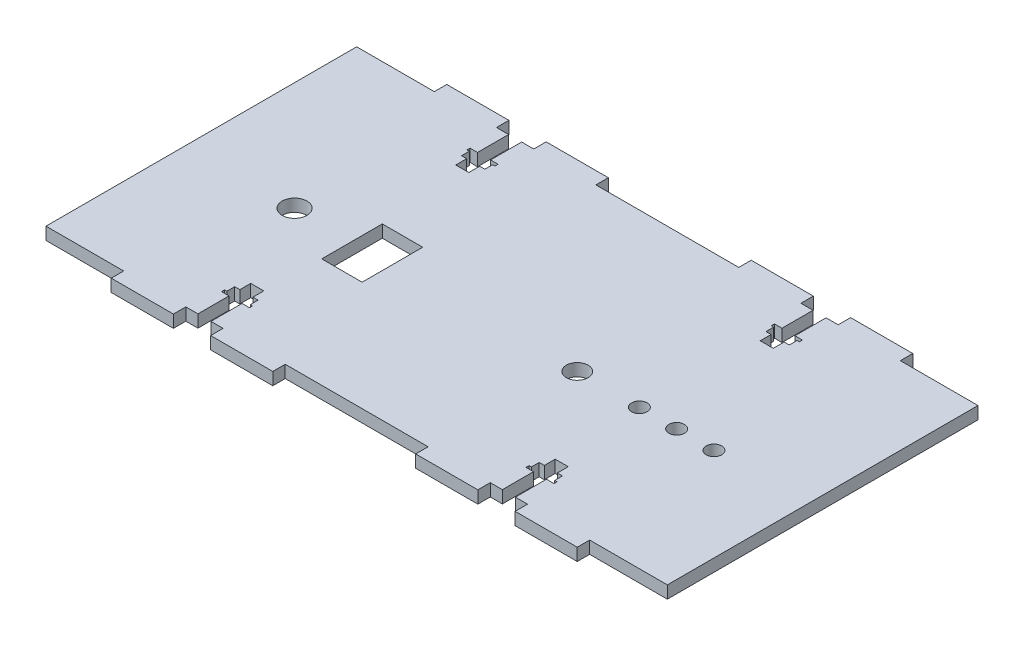
SolidWorks part; units mm, degrees
ref_plane "Front Plane" through (0, 0, 0) normal (0, 0, 1) x (1, 0, 0)
ref_plane "Top Plane" through (0, 0, 0) normal (0, 1, 0) x (1, 0, 0)
ref_plane "Right Plane" through (0, 0, 0) normal (1, 0, 0) x (0, 0, -1)
sketch "Sketch1" plane through (0, 0, 0) normal (0, 1, 0) x (1, 0, 0)
  line L0 (-55, -50) -> (-43, -50)
  line L1 (0, 0) -> (199.9733, 0) construction
  line L2 (-100, -50) -> (-100, 50)
  line L3 (-100, -50) -> (-75, -50)
  line L4 (100, -50) -> (100, 50)
  line L5 (0, 0) -> (100, -50) construction
  line L6 (-100, -50) -> (0, 0) construction
  line L7 (-23, -50) -> (23, -50)
  line L8 (-75, -50) -> (-75, -54)
  line L9 (-75, -54) -> (-55, -54)
  line L10 (-55, -50) -> (-55, -54)
  line L11 (43, -50) -> (55, -50)
  line L12 (-43, -50) -> (-43, -54)
  line L13 (-43, -54) -> (-23, -54)
  line L14 (-23, -50) -> (-23, -54)
  line L15 (-100, 50) -> (0, 0) construction
  line L16 (75, -50) -> (75, -54)
  line L17 (75, -54) -> (55, -54)
  line L18 (55, -50) -> (55, -54)
  line L19 (75, -50) -> (100, -50)
  line L20 (43, -50) -> (43, -54)
  line L21 (43, -54) -> (23, -54)
  line L22 (23, -50) -> (23, -54)
  line L23 (0, 0) -> (100, 50) construction
  line L24 (23, 50) -> (23, 54)
  line L25 (43, 54) -> (23, 54)
  line L26 (43, 50) -> (43, 54)
  line L27 (75, 50) -> (100, 50)
  line L28 (55, 50) -> (55, 54)
  line L29 (75, 54) -> (55, 54)
  line L30 (75, 50) -> (75, 54)
  line L31 (-23, 50) -> (-23, 54)
  line L32 (-43, 54) -> (-23, 54)
  line L33 (-43, 50) -> (-43, 54)
  line L34 (43, 50) -> (55, 50)
  line L35 (-55, 50) -> (-55, 54)
  line L36 (-75, 54) -> (-55, 54)
  line L37 (-75, 50) -> (-75, 54)
  line L38 (-23, 50) -> (23, 50)
  line L39 (-100, 50) -> (-75, 50)
  line L40 (-55, 50) -> (-43, 50)
  point P0 (0, 0)
  point P25 (-100, 0)
  point P43 (100, 0)
  dimension "D2" = 200
  dimension "D3" = 50
  dimension "D4" = 20
  dimension "D5" = 12
  dimension "D6" = 20
  dimension "D7" = 4
  dimension "D8" = 12
  dimension "D9" = 20
  dimension "D10" = 20
  dimension "D11" = 25
  dimension "D12" = 4
  dimension "D13" = 25
extrude "Boss-Extrude1" add sketch "Sketch1" along normal blind 4
sketch "Sketch2" plane through (0, 0, 0) normal (0, -1, 0) x (1, 0, 0)
  line L0 (-100, 5) -> (100, 5) construction
  line L1 (-46.5, 14.75) -> (-33.5, 14.75)
  line L2 (-46.5, 14.75) -> (-46.5, -4.75)
  line L3 (-46.5, -4.75) -> (-33.5, -4.75)
  line L4 (-33.5, 14.75) -> (-33.5, -4.75)
  line L5 (-46.5, 14.75) -> (-33.5, -4.75) construction
  line L6 (-46.5, -4.75) -> (-33.5, 14.75) construction
  line L7 (-100, -50) -> (-100, 50) construction
  line L8 (100, 50) -> (100, -50) construction
  line L9 (-100, 50) -> (-75, 50) construction
  circle A0 centre (-65, 5) radius 4
  circle A1 centre (26, 5) radius 3.5
  circle A2 centre (46, 5) radius 2.5
  circle A3 centre (58, 5) radius 2.5
  circle A4 centre (70, 5) radius 2.5
  point P2 (-40, 5)
  dimension "D1" = 8
  dimension "D6" = 7
  dimension "D7" = 5
  dimension "D2" = 13
  dimension "D3" = 19.5
  dimension "D4" = 25
  dimension "D5" = 35
  dimension "D9" = 20
  dimension "D10" = 45
  dimension "D11" = 12
  dimension "D12" = 30
  dimension "D8" = 3
extrude "Cut-Extrude1" cut sketch "Sketch2" against normal through all
sketch "Sketch3" plane through (0, 0, 0) normal (0, -1, 0) x (1, 0, 0)
  line L0 (-43, -50) -> (-55, -50) construction
  line L1 (-51.1, -50) -> (-46.9, -50)
  line L2 (-51.1, -50) -> (-51.1, -40)
  line L3 (-51.1, -33) -> (-46.9, -33)
  line L4 (-46.9, -50) -> (-46.9, -40)
  line L5 (-55, -50) -> (-55, -54) construction
  line L6 (-49, -50) -> (-49, -33) construction
  line L7 (-52.75, -36.5) -> (-51.1, -36.5)
  line L8 (-52.75, -36.5) -> (-52.75, -39)
  line L9 (-46.9, -36.5) -> (-46.9, -33)
  line L10 (-45.25, -36.5) -> (-45.25, -39)
  line L11 (-53.5, -39) -> (-53.5, -40)
  line L12 (-44.5, -40) -> (-46.9, -40)
  line L13 (0, -50) -> (0, -26.0736) construction
  line L14 (23, -50) -> (-23, -50) construction
  line L15 (-46.9, -40) -> (-44.5, -40)
  line L16 (-44.5, -39) -> (-44.5, -40)
  line L17 (-44.5, -39) -> (-45.25, -39)
  line L18 (-46.9, -36.5) -> (-46.9, -33)
  line L19 (-45.25, -39) -> (-44.5, -39)
  line L20 (-51.1, -36.5) -> (-52.75, -36.5)
  line L21 (-52.75, -39) -> (-53.5, -39)
  line L22 (-46.9, -36.5) -> (-45.25, -36.5)
  line L23 (-51.1, -36.5) -> (-51.1, -33)
  line L24 (-51.1, -40) -> (-53.5, -40)
  line L25 (-52.75, -36.5) -> (-52.75, -39)
  line L26 (-51.1, -36.5) -> (-51.1, -33)
  line L27 (-53.5, -39) -> (-52.75, -39)
  line L28 (-53.5, -39) -> (-53.5, -40)
  line L29 (-53.5, -40) -> (-51.1, -40)
  line L30 (-44.5, -39) -> (-44.5, -40)
  line L31 (-45.25, -36.5) -> (-45.25, -39)
  line L32 (-45.25, -36.5) -> (-46.9, -36.5)
  line L33 (-51.1, -50) -> (-51.1, -40)
  line L34 (-46.9, -50) -> (-46.9, -40)
  line L35 (-51.1, -50) -> (-51.1, -40)
  line L36 (-46.9, -50) -> (-46.9, -40)
  line L37 (-52.75, -36.5) -> (-51.1, -36.5)
  line L38 (-52.75, -36.5) -> (-52.75, -39)
  line L39 (-53.5, -39) -> (-53.5, -40)
  line L40 (-44.5, -40) -> (-46.9, -40)
  line L41 (-44.5, -39) -> (-44.5, -40)
  line L42 (-44.5, -39) -> (-45.25, -39)
  line L43 (-46.9, -36.5) -> (-46.9, -33)
  line L44 (-45.25, -36.5) -> (-45.25, -39)
  line L45 (-46.9, -40) -> (-44.5, -40)
  line L46 (-46.9, -36.5) -> (-46.9, -33)
  line L47 (-51.1, -36.5) -> (-52.75, -36.5)
  line L48 (-45.25, -39) -> (-44.5, -39)
  line L49 (-46.9, -36.5) -> (-45.25, -36.5)
  line L50 (-52.75, -39) -> (-53.5, -39)
  line L51 (-51.1, -36.5) -> (-51.1, -33)
  line L52 (-53.5, -39) -> (-52.75, -39)
  line L53 (-53.5, -39) -> (-53.5, -40)
  line L54 (-51.1, -40) -> (-53.5, -40)
  line L55 (-53.5, -40) -> (-51.1, -40)
  line L56 (-44.5, -39) -> (-44.5, -40)
  line L57 (-52.75, -36.5) -> (-52.75, -39)
  line L58 (-51.1, -36.5) -> (-51.1, -33)
  line L59 (-45.25, -36.5) -> (-45.25, -39)
  line L60 (-45.25, -36.5) -> (-46.9, -36.5)
  line L61 (-51.1, -50) -> (-51.1, -40)
  line L62 (-46.9, -50) -> (-46.9, -40)
  line L63 (49, -50) -> (49, -33) construction
  line L64 (46.9, -50) -> (46.9, -40)
  line L65 (51.1, -50) -> (51.1, -40)
  line L66 (45.25, -36.5) -> (46.9, -36.5)
  line L67 (45.25, -36.5) -> (45.25, -39)
  line L68 (51.1, -36.5) -> (51.1, -33)
  line L69 (52.75, -36.5) -> (52.75, -39)
  line L70 (44.5, -39) -> (44.5, -40)
  line L71 (53.5, -40) -> (51.1, -40)
  line L72 (51.1, -40) -> (53.5, -40)
  line L73 (53.5, -39) -> (53.5, -40)
  line L74 (53.5, -39) -> (52.75, -39)
  line L75 (51.1, -36.5) -> (51.1, -33)
  line L76 (52.75, -39) -> (53.5, -39)
  line L77 (46.9, -36.5) -> (45.25, -36.5)
  line L78 (45.25, -39) -> (44.5, -39)
  line L79 (51.1, -36.5) -> (52.75, -36.5)
  line L80 (46.9, -36.5) -> (46.9, -33)
  line L81 (46.9, -40) -> (44.5, -40)
  line L82 (45.25, -36.5) -> (45.25, -39)
  line L83 (46.9, -36.5) -> (46.9, -33)
  line L84 (44.5, -39) -> (45.25, -39)
  line L85 (44.5, -39) -> (44.5, -40)
  line L86 (44.5, -40) -> (46.9, -40)
  line L87 (53.5, -39) -> (53.5, -40)
  line L88 (52.75, -36.5) -> (52.75, -39)
  line L89 (52.75, -36.5) -> (51.1, -36.5)
  line L90 (46.9, -50) -> (46.9, -40)
  line L91 (51.1, -50) -> (51.1, -40)
  line L92 (46.9, -50) -> (46.9, -40)
  line L93 (51.1, -50) -> (51.1, -40)
  line L94 (45.25, -36.5) -> (46.9, -36.5)
  line L95 (45.25, -36.5) -> (45.25, -39)
  line L96 (44.5, -39) -> (44.5, -40)
  line L97 (53.5, -40) -> (51.1, -40)
  line L98 (53.5, -39) -> (53.5, -40)
  line L99 (53.5, -39) -> (52.75, -39)
  line L100 (51.1, -36.5) -> (51.1, -33)
  line L101 (52.75, -36.5) -> (52.75, -39)
  line L102 (51.1, -40) -> (53.5, -40)
  line L103 (51.1, -36.5) -> (51.1, -33)
  line L104 (46.9, -36.5) -> (45.25, -36.5)
  line L105 (52.75, -39) -> (53.5, -39)
  line L106 (51.1, -36.5) -> (52.75, -36.5)
  line L107 (45.25, -39) -> (44.5, -39)
  line L108 (46.9, -36.5) -> (46.9, -33)
  line L109 (44.5, -39) -> (45.25, -39)
  line L110 (44.5, -39) -> (44.5, -40)
  line L111 (46.9, -40) -> (44.5, -40)
  line L112 (44.5, -40) -> (46.9, -40)
  line L113 (53.5, -39) -> (53.5, -40)
  line L114 (45.25, -36.5) -> (45.25, -39)
  line L115 (46.9, -36.5) -> (46.9, -33)
  line L116 (52.75, -36.5) -> (52.75, -39)
  line L117 (52.75, -36.5) -> (51.1, -36.5)
  line L118 (46.9, -50) -> (46.9, -40)
  line L119 (51.1, -33) -> (46.9, -33)
  line L120 (51.1, -50) -> (51.1, -40)
  line L121 (51.1, -50) -> (46.9, -50)
  point P47 (49, -43.5)
  point P48 (49, -41.75)
  dimension "D1" = 4.2
  dimension "D2" = 17
  dimension "D3" = 3.9
  dimension "D4" = 7.5
  dimension "D5" = 2.5
  dimension "D6" = 1
  dimension "D7" = 10
  dimension "D8" = 9
extrude "Cut-Extrude2" cut sketch "Sketch3" against normal blind 6
mirror "Mirror1" about plane through (0, 0, 0) normal (0, 0, 1) of "Cut-Extrude2"
equation "\"D3@Sketch3\" = (12-\"D1@Sketch3\")/2"
